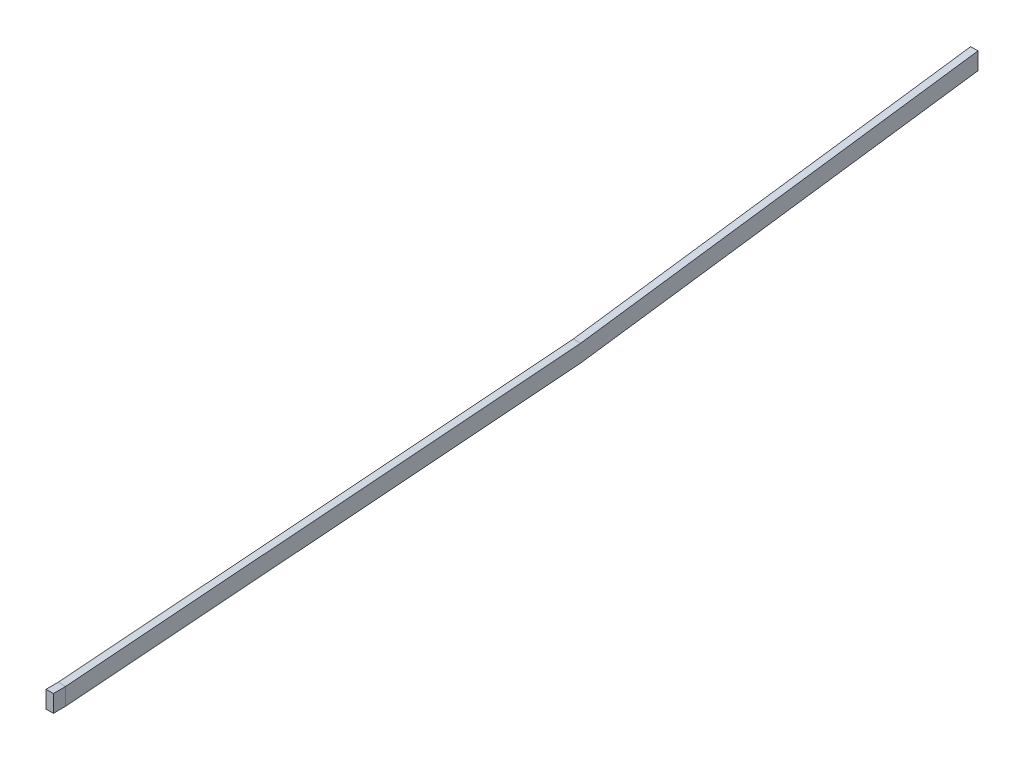
SolidWorks part; units mm, degrees
ref_plane "Front Plane" through (0, 0, 0) normal (0, 0, 1) x (1, 0, 0)
ref_plane "Top Plane" through (0, 0, 0) normal (0, 1, 0) x (1, 0, 0)
ref_plane "Right Plane" through (0, 0, 0) normal (1, 0, 0) x (0, 0, -1)
sketch "Sketch1" plane through (0, 0, 0) normal (1, 0, 0) x (0, 0, -1)
  line L0 (0, 0) -> (0, 7)
  line L1 (0, 0) -> (210, 16.1955)
  line L2 (210, 16.1955) -> (372, 38.4155)
  line L3 (0, 7) -> (210, 23.1955)
  line L4 (210, 23.1955) -> (372, 45.4155)
  line L5 (372, 45.4155) -> (372, 38.4155)
  line L6 (210, 16.1955) -> (210, 23.1955) construction
  dimension "D1" = 7
  dimension "D2" = 85.59
  dimension "D3" = 176.6
  dimension "D4" = 210
  dimension "D5" = 372
  dimension "D6" = 7
  dimension "D7" = 7
extrude "Boss-Extrude1" add sketch "Sketch1" along normal blind 3
sketch "Sketch2" plane through (3, 0, 0) normal (1, 0, 0) x (0, 0, -1)
  line L1 (0, 0) -> (-5, 0)
  line L2 (0, 0) -> (0, 7)
  line L3 (0, 7) -> (-5, 7)
  line L4 (-5, 0) -> (-5, 7)
  dimension "D1" = 5
extrude "Boss-Extrude2" add sketch "Sketch2" against normal blind 3 separate body
